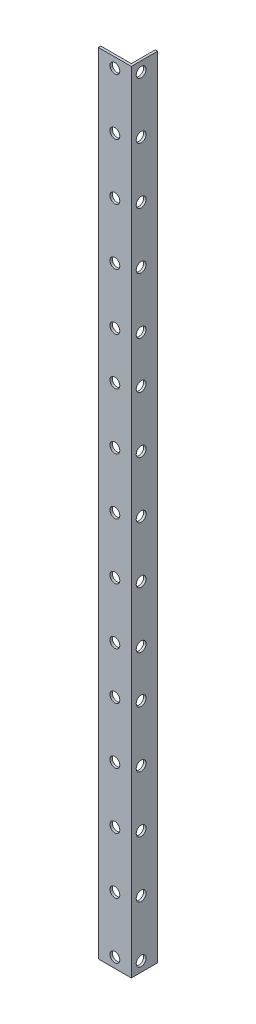
SolidWorks part; units mm, degrees
material "6061-T6 (SS)"
ref_plane "Alzado" through (0, 0, 0) normal (0, 0, 1) x (1, 0, 0)
ref_plane "Planta" through (0, 0, 0) normal (0, 1, 0) x (1, 0, 0)
ref_plane "Vista lateral" through (0, 0, 0) normal (1, 0, 0) x (0, 0, -1)
sketch "Sketch1" plane through (0, 0, 0) normal (0, 1, 0) x (1, 0, 0)
  line L0 (0, 0) -> (15, 0)
  line L1 (15, 0) -> (15, 12)
  line L2 (15, 12) -> (13.9, 12)
  line L3 (13.9, 12) -> (13.9, 1.1)
  line L4 (13.9, 1.1) -> (0, 1.1)
  line L5 (0, 1.1) -> (0, 0)
  dimension "D1" = 15
  dimension "D2" = 12
  dimension "D3" = 1.1
  dimension "D4" = 1.1
extrude "Boss-Extrude1" add sketch "Sketch1" along normal blind 360
sketch "Sketch2" plane through (13.9, 0, 0) normal (-1, 0, 0) x (0, 0, 1)
  circle A1 centre (-4.5, 329.8125) radius 2.25
  circle A2 centre (-4.5, 304.125) radius 2.25
  circle A3 centre (-4.5, 278.4375) radius 2.25
  circle A4 centre (-4.5, 252.75) radius 2.25
  circle A5 centre (-4.5, 231.375) radius 2.25
  circle A6 centre (-4.5, 205.6875) radius 2.25
  circle A7 centre (-4.5, 180) radius 2.25
  circle A8 centre (-4.5, 154.3125) radius 2.25
  circle A9 centre (-4.5, 128.625) radius 2.25
  circle A10 centre (-4.5, 107.25) radius 2.25
  circle A11 centre (-4.5, 81.5625) radius 2.25
  circle A12 centre (-4.5, 55.875) radius 2.25
  circle A13 centre (-4.5, 30.1875) radius 2.25
  circle A14 centre (-4.5, 4.5) radius 2.25
  circle A15 centre (-4.5, 355.5) radius 2.25
  dimension "D1" = 4.5
extrude "Cut-Extrude1" cut sketch "Sketch2" against normal up to next
sketch "Sketch3" plane through (0, 0, 0) normal (0, 0, 1) x (1, 0, 0)
  line L0 (-218, 242.75) -> (18, 242.75) construction
  line L2 (18, 363) -> (18, -3) construction
  line L3 (-65, 263) -> (-10, 263) construction
  line L4 (-10, 222.5) -> (-65, 222.5) construction
  line L5 (-218, 117.25) -> (18, 117.25) construction
  line L6 (-218, -3) -> (-218, 363) construction
  line L7 (-65, 137.5) -> (-10, 137.5) construction
  line L8 (-10, 97) -> (-65, 97) construction
  circle A15 centre (7.5, 355.5) radius 2.25
  dimension "D1" = 4.5
extrude "Cut-Extrude2" cut sketch "Sketch3" against normal up to next (1.1 mm away)
sketch "Sketch4" plane through (0, 0, 0) normal (0, 0, 1) x (1, 0, 0)
  line L0 (18, 242.75) -> (-100, 242.75) construction
  line L1 (-218, 242.75) -> (18, 242.75) construction
  line L2 (18, 117.25) -> (-100, 117.25) construction
  line L3 (-218, 117.25) -> (18, 117.25) construction
pattern_linear "LPattern1" count 5 spacing 25.6562 along (0, -1, 0) of "Cut-Extrude2"
pattern_linear "LPattern2" count 3 spacing 124.1875 along (0, -1, 0) of "LPattern1", "Cut-Extrude2"
